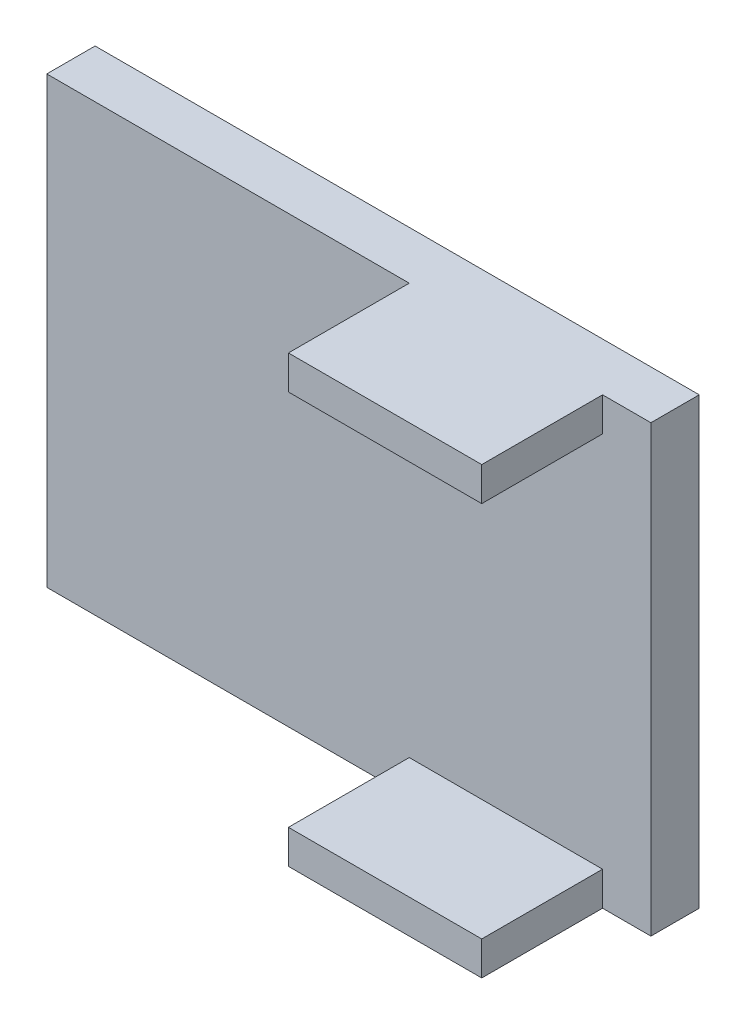
SolidWorks part; units mm, degrees
material "PPE"
ref_plane "Front Plane" through (0, 0, 0) normal (0, 0, 1) x (1, 0, 0)
ref_plane "Top Plane" through (0, 0, 0) normal (0, 1, 0) x (1, 0, 0)
ref_plane "Right Plane" through (0, 0, 0) normal (1, 0, 0) x (0, 0, -1)
sketch "Sketch2" plane through (0, 0, 0) normal (0, 0, 1) x (1, 0, 0)
  line L1 (-15.875, -11.684) -> (15.875, -11.684)
  line L2 (-15.875, -11.684) -> (-15.875, 11.684)
  line L3 (-15.875, 11.684) -> (15.875, 11.684)
  line L4 (15.875, -11.684) -> (15.875, 11.684)
  line L5 (-15.875, -11.684) -> (15.875, 11.684) construction
  line L6 (-15.875, 11.684) -> (15.875, -11.684) construction
  point P0 (0, 0)
  dimension "D1" = 31.75
  dimension "D2" = 23.368
extrude "Boss-Extrude1" add sketch "Sketch2" along normal blind 2.54
sketch "Sketch3" plane through (0, 0, 2.54) normal (0, 0, 1) x (1, 0, 0)
  line L0 (15.875, -11.684) -> (15.875, 11.684) construction
  line L3 (3.175, 9.906) -> (3.175, -9.906) construction
  line L4 (15.875, 11.684) -> (3.175, 11.684)
  line L5 (15.875, 11.684) -> (15.875, 9.906)
  line L6 (15.875, 9.906) -> (3.175, 9.906)
  line L7 (3.175, 11.684) -> (3.175, 9.906)
  line L8 (15.875, -11.684) -> (3.175, -11.684)
  line L9 (15.875, -11.684) -> (15.875, -9.906)
  line L10 (15.875, -9.906) -> (3.175, -9.906)
  line L11 (3.175, -11.684) -> (3.175, -9.906)
  dimension "D1" = 19.812
  dimension "D2" = 12.7
extrude "Boss-Extrude2" add sketch "Sketch3" along normal blind 6.35
sketch "Sketch4" plane through (0, 11.684, 0) normal (0, 1, 0) x (1, 0, 0)
  line L1 (15.875, -8.89) -> (13.335, -8.89)
  line L2 (15.875, -8.89) -> (15.875, -2.54)
  line L3 (15.875, -2.54) -> (13.335, -2.54)
  line L4 (13.335, -8.89) -> (13.335, -2.54)
  dimension "D1" = 6.35
  dimension "D2" = 2.54
extrude "Cut-Extrude1" cut sketch "Sketch4" against normal through all
scale "Scale1" [suppressed]
